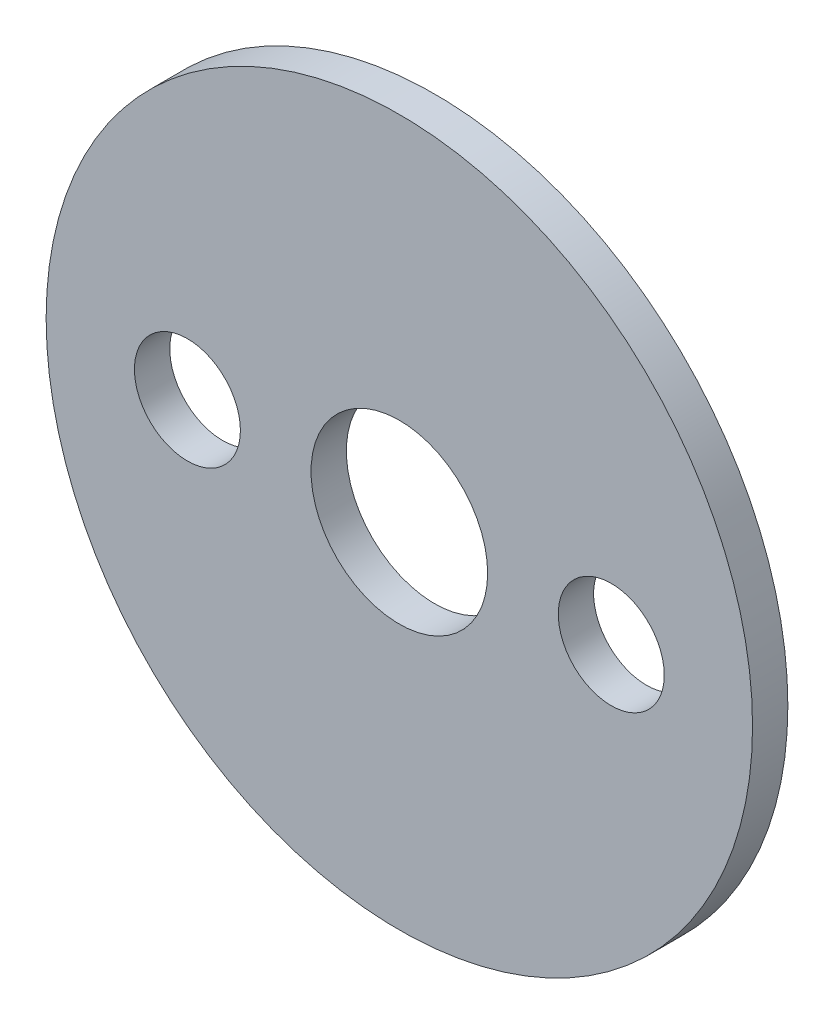
SolidWorks part; units mm, degrees
ref_plane "Front Plane" through (0, 0, 0) normal (0, 0, 1) x (1, 0, 0)
ref_plane "Top Plane" through (0, 0, 0) normal (0, 1, 0) x (1, 0, 0)
ref_plane "Right Plane" through (0, 0, 0) normal (1, 0, 0) x (0, 0, -1)
sketch "Croquis1" plane through (0, 0, 0) normal (0, 0, 1) x (1, 0, 0)
  circle A0 centre (0, 0) radius 2.5
  circle A1 centre (0, 0) radius 0.625
  dimension "D1" = 5
  dimension "D2" = 1.25
extrude "Saliente-Extruir1" add sketch "Croquis1" along normal blind 0.25
hole_wizard "Taladro roscado M1x0.251" positions "Croquis3" profile "Croquis2" tap size "M1x0.25" standard "KS" end condition through all
sketch "Croquis3" plane through (0, 0, 0.25) normal (0, 0, 1) x (1, 0, 0)
  point P0 (-1.5, 0)
  point P1 (1.5, 0)
  dimension "D1" = 3
  dimension "D2" = 1.5
sketch "Croquis2" plane through (-1.5, 0, 0.25) normal (1, 0, 0) x (0, -1, 0)
  line L0 (0, 0) -> (0, 0.25)
  line L1 (0, 0.25) -> (0.375, 0.25)
  line L2 (0.375, 0.25) -> (0.375, 0)
  line L5 (0.375, 0) -> (0, 0)
  line L11 (0, -6.35) -> (0, 107.95) construction
  dimension "Diámetro de perforador para roscar hasta el siguiente" = 0.75
  dimension "Profundidad de perforador para roscar hasta el siguiente" = 0.25
cosmetic thread "Rosca de taladro1" parameters "D2"=1
cosmetic thread "Rosca de taladro2" parameters "D2"=1
